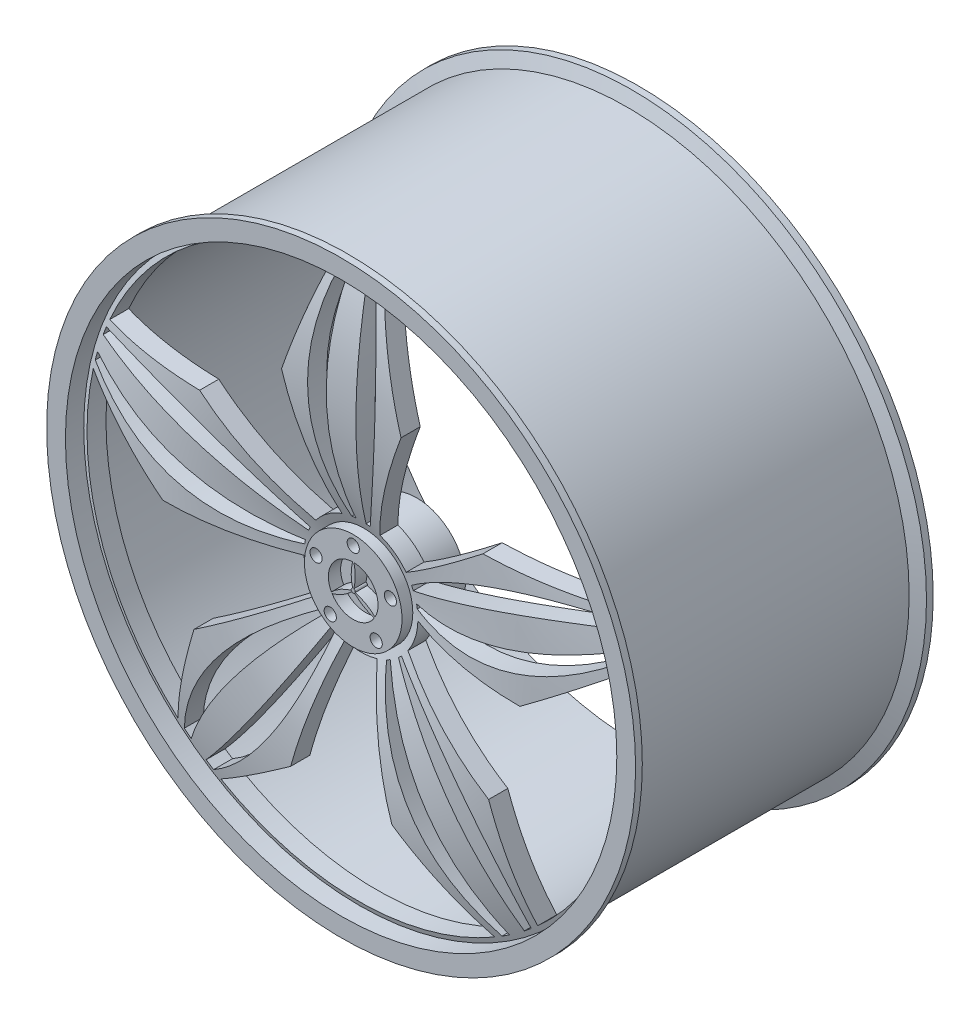
SolidWorks part; units mm, degrees
ref_plane "Front Plane" through (0, 0, 0) normal (0, 0, 1) x (1, 0, 0)
ref_plane "Top Plane" through (0, 0, 0) normal (0, 1, 0) x (1, 0, 0)
ref_plane "Right Plane" through (0, 0, 0) normal (1, 0, 0) x (0, 0, -1)
sketch "Sketch1" plane through (0, 0, 0) normal (0, 0, 1) x (1, 0, 0)
  circle A0 centre (0, 0) radius 225.9
  dimension "D1" = 451.8
sketch "Sketch2" plane through (0, 0, 0) normal (1, 0, 0) x (0, 0, -1)
  line L0 (112.7186, 230.7873) -> (-112.7186, 230.7873)
  line L1 (0, 55) -> (0, -55) construction
  line L2 (-112.7186, 230.7873) -> (-116.422, 241.3)
  line L3 (-116.422, 241.3) -> (-121.92, 241.3)
  line L4 (-121.92, 241.3) -> (-121.92, 225.9)
  line L6 (112.7186, 230.7873) -> (116.422, 241.3)
  line L7 (116.422, 241.3) -> (121.92, 241.3)
  line L8 (121.92, 241.3) -> (121.92, 225.9)
  line L10 (-121.92, 225.9) -> (121.92, 225.9)
  point P5 (0, 230.7873)
  dimension "D1" = 15.4
  dimension "D2" = 243.84
sketch "Sketch4" plane through (0, 0, 0) normal (1, 0, 0) x (0, 0, -1)
  line L0 (-133.5047, 0) -> (160.5273, 0)
revolve "Revolve1" add sketch "Sketch2" angle 360 about L0
ref_plane "Plane1" through (0, 0, 60) normal (0, 0, 1) x (1, 0, 0)
sketch "Sketch5" plane through (0, 0, 60) normal (0, 0, 1) x (1, 0, 0)
  circle A0 centre (0, 0) radius 40
extrude "Boss-Extrude1" add sketch "Sketch5" along normal blind 52 separate body
sketch "Sketch6" plane through (0, 0, 0) normal (1, 0, 0) x (0, 0, -1)
  line L0 (-121.92, 225.9) -> (-121.92, -225.9) construction
  line L1 (-106.2027, 227.9587) -> (-90.7146, 227.9587)
  line L2 (-102.0002, 36.9898) -> (-87.5596, 36.9898)
  spline S0 degree 2 poles (-102.0002, 36.9898) (-139.6143, 132.0927) (-106.2027, 227.9587) knots 0 0 0 1 1 1
  spline S1 degree 2 poles (-87.5596, 36.9898) (-123.2013, 132.2737) (-90.7146, 227.9587) knots 0 0 0 1 1 1
revolve "Revolve2" add sketch "Sketch6" angle 360 about L0
sketch "Sketch9" plane through (0, 0, 112) normal (0, 0, 1) x (1, 0, 0)
  circle A0 centre (0, 32.0205) radius 5
  circle A1 centre (30.4533, 9.8949) radius 5
  circle A2 centre (18.8212, -25.9051) radius 5
  circle A3 centre (-18.8212, -25.9051) radius 5
  circle A4 centre (-30.4533, 9.8949) radius 5
  point P12 (0, 0)
  dimension "D1" = 5
extrude "Cut-Extrude1" cut sketch "Sketch9" against normal blind 102
ref_plane "Plane2" through (0, 0, 130) normal (0, 0, 1) x (1, 0, 0)
sketch "Sketch10" plane through (0, 0, 130) normal (0, 0, 1) x (1, 0, 0)
  line L0 (116.0715, 89.196) -> (203.2814, 88.9532)
  line L1 (-15.6066, 43.9722) -> (-48.9624, 137.9536)
  line L2 (-48.9624, 137.9536) -> (-21.7821, 220.8202)
  line L3 (15.6066, 43.9722) -> (48.9624, 137.9536)
  line L4 (48.9624, 137.9536) -> (21.7821, 220.8202)
  line L5 (36.9974, 28.4309) -> (116.0715, 89.196)
  line L6 (46.6428, -1.2546) -> (146.3319, -3.936)
  line L7 (146.3319, -3.936) -> (216.7435, 47.5212)
  line L8 (120.6985, -82.8275) -> (147.4169, -165.8441)
  line L9 (38.4722, -26.401) -> (120.6985, -82.8275)
  line L10 (13.2202, -44.7476) -> (41.4757, -140.3862)
  line L11 (41.4757, -140.3862) -> (112.1728, -191.4504)
  line L12 (-41.4757, -140.3862) -> (-112.1728, -191.4504)
  line L13 (-13.2202, -44.7476) -> (-41.4757, -140.3862)
  line L14 (-38.4722, -26.401) -> (-120.6985, -82.8275)
  line L15 (-120.6985, -82.8275) -> (-147.4169, -165.8441)
  line L16 (-146.3319, -3.936) -> (-216.7435, 47.5212)
  line L17 (-46.6428, -1.2546) -> (-146.3319, -3.936)
  line L18 (-36.9974, 28.4309) -> (-116.0715, 89.196)
  line L19 (-116.0715, 89.196) -> (-203.2814, 88.9532)
  arc A0 (-15.6066, 43.9722) -> (-36.9974, 28.4309) centre (0, 0) ccw
  arc A1 (-21.7821, 220.8202) -> (-203.2814, 88.9532) centre (0, 0) ccw
  arc A2 (-7.5398, 221.7637) -> (-14.8027, 221.3976) centre (0, 0) ccw
  arc A3 (14.8027, 221.3976) -> (7.5398, 221.7637) centre (0, 0) ccw
  arc A4 (-4.1675, 46.4732) -> (-7.5398, 46.0464) centre (0, 0) ccw
  arc A5 (7.5398, 46.0464) -> (4.1675, 46.4732) centre (0, 0) ccw
  arc A6 (36.9974, 28.4309) -> (15.6066, 43.9722) centre (0, 0) ccw
  arc A7 (42.9108, 18.3246) -> (41.4628, 21.3999) centre (0, 0) ccw
  arc A8 (46.1227, 7.0583) -> (45.4864, 10.3974) centre (0, 0) ccw
  arc A9 (38.4722, -26.401) -> (46.6428, -1.2546) centre (0, 0) ccw
  arc A10 (30.6878, -35.148) -> (33.1653, -32.8205) centre (0, 0) ccw
  arc A11 (20.9656, -41.6841) -> (23.9446, -40.0472) centre (0, 0) ccw
  arc A12 (-13.2202, -44.7476) -> (13.2202, -44.7476) centre (0, 0) ccw
  arc A13 (-23.9446, -40.0472) -> (-20.9656, -41.6841) centre (0, 0) ccw
  arc A14 (-33.1653, -32.8205) -> (-30.6878, -35.148) centre (0, 0) ccw
  arc A15 (-46.6428, -1.2546) -> (-38.4722, -26.401) centre (0, 0) ccw
  arc A16 (-45.4864, 10.3974) -> (-46.1227, 7.0583) centre (0, 0) ccw
  arc A17 (-41.4628, 21.3999) -> (-42.9108, 18.3246) centre (0, 0) ccw
  arc A18 (203.2814, 88.9532) -> (21.7821, 220.8202) centre (0, 0) ccw
  arc A19 (208.5799, 75.6996) -> (205.9873, 82.4938) centre (0, 0) ccw
  arc A20 (215.1359, 54.3374) -> (213.2398, 61.358) centre (0, 0) ccw
  arc A21 (118.1586, -187.8152) -> (124.2496, -183.8424) centre (0, 0) ccw
  arc A22 (136.4493, -174.9788) -> (142.1098, -170.4136) centre (0, 0) ccw
  arc A23 (147.4169, -165.8441) -> (216.7435, 47.5212) centre (0, 0) ccw
  arc A24 (-142.1098, -170.4136) -> (-136.4493, -174.9788) centre (0, 0) ccw
  arc A25 (-124.2496, -183.8424) -> (-118.1586, -187.8152) centre (0, 0) ccw
  arc A26 (-112.1728, -191.4504) -> (112.1728, -191.4504) centre (0, 0) ccw
  arc A27 (-216.7435, 47.5212) -> (-147.4169, -165.8441) centre (0, 0) ccw
  arc A28 (-213.2398, 61.358) -> (-215.1359, 54.3374) centre (0, 0) ccw
  arc A29 (-205.9873, 82.4938) -> (-208.5799, 75.6996) centre (0, 0) ccw
  spline S0 degree 2 poles (-7.5398, 46.0464) (-43.6195, 132.703) (-14.8027, 221.3976) knots 0 0 0 1 1 1
  spline S1 degree 2 poles (-4.1675, 46.4732) (-18.32, 133.9184) (-7.5398, 221.7637) knots 0 0 0 1 1 1
  spline S2 degree 2 poles (4.1675, 46.4732) (18.32, 133.9184) (7.5398, 221.7637) knots 0 0 0 1 1 1
  spline S3 degree 2 poles (7.5398, 46.0464) (43.6195, 132.703) (14.8027, 221.3976) knots 0 0 0 1 1 1
  spline S4 degree 2 poles (41.4628, 21.3999) (112.7289, 82.492) (205.9873, 82.4938) knots 0 0 0 1 1 1
  spline S5 degree 2 poles (42.9108, 18.3246) (121.7028, 58.8064) (208.5799, 75.6996) knots 0 0 0 1 1 1
  spline S6 degree 2 poles (45.4864, 10.3974) (133.0252, 23.9598) (213.2398, 61.358) knots 0 0 0 1 1 1
  spline S7 degree 2 poles (46.1227, 7.0583) (139.6872, -0.4771) (215.1359, 54.3374) knots 0 0 0 1 1 1
  spline S8 degree 2 poles (33.1653, -32.8205) (113.2897, -81.7201) (142.1098, -170.4136) knots 0 0 0 1 1 1
  spline S9 degree 2 poles (30.6878, -35.148) (93.5364, -97.5741) (136.4493, -174.9788) knots 0 0 0 1 1 1
  spline S10 degree 2 poles (23.9446, -40.0472) (63.8941, -119.1105) (124.2496, -183.8424) knots 0 0 0 1 1 1
  spline S11 degree 2 poles (20.9656, -41.6841) (42.712, -132.9978) (118.1586, -187.8152) knots 0 0 0 1 1 1
  spline S12 degree 2 poles (-20.9656, -41.6841) (-42.712, -132.9978) (-118.1586, -187.8152) knots 0 0 0 1 1 1
  spline S13 degree 2 poles (-23.9446, -40.0472) (-63.8941, -119.1105) (-124.2496, -183.8424) knots 0 0 0 1 1 1
  spline S14 degree 2 poles (-30.6878, -35.148) (-93.5364, -97.5741) (-136.4493, -174.9788) knots 0 0 0 1 1 1
  spline S15 degree 2 poles (-33.1653, -32.8205) (-113.2897, -81.7201) (-142.1098, -170.4136) knots 0 0 0 1 1 1
  spline S16 degree 2 poles (-46.1227, 7.0583) (-139.6872, -0.4771) (-215.1359, 54.3374) knots 0 0 0 1 1 1
  spline S17 degree 2 poles (-45.4864, 10.3974) (-133.0252, 23.9598) (-213.2398, 61.358) knots 0 0 0 1 1 1
  spline S18 degree 2 poles (-42.9108, 18.3246) (-121.7028, 58.8064) (-208.5799, 75.6996) knots 0 0 0 1 1 1
  spline S19 degree 2 poles (-41.4628, 21.3999) (-112.7289, 82.492) (-205.9873, 82.4938) knots 0 0 0 1 1 1
  point P96 (0, 0)
  dimension "D1" = 5
extrude "Cut-Extrude2" cut sketch "Sketch10" against normal blind 448
sketch "Sketch11" plane through (0, 0, 112) normal (0, 0, 1) x (1, 0, 0)
  circle A0 centre (0, 0) radius 21
  circle A1 centre (0, 0) radius 1.2557
  arc A2 (-0.4876, 20.331) -> (-17.8623, -9.7225) centre (0, 0) ccw
  circle A3 centre (0, 0) radius 1.6581
  arc A4 (-17.3634, -10.5878) -> (17.3511, -10.608) centre (0, 0) ccw
  arc A5 (17.851, -9.7432) -> (0.5113, 20.3305) centre (0, 0) ccw
  spline S0 degree 2 poles (-0.4502, 1.5958) (-2.8593, 10.9394) (-0.4876, 20.331) knots 0 0 0 1 1 1
  spline S1 degree 2 poles (0.4502, 1.5958) (2.8488, 10.9366) (0.5113, 20.3305) knots 0 0 0 1 1 1
  spline S2 degree 2 poles (1.6071, -0.4081) (10.9034, -2.9935) (17.851, -9.7432) knots 0 0 0 1 1 1
  spline S3 degree 2 poles (1.157, -1.1878) (8.0469, -7.9354) (17.3511, -10.608) knots 0 0 0 1 1 1
  spline S4 degree 2 poles (-1.157, -1.1878) (-8.0442, -7.9459) (-17.3634, -10.5878) knots 0 0 0 1 1 1
  spline S5 degree 2 poles (-1.6071, -0.4081) (-10.8957, -3.0011) (-17.8623, -9.7225) knots 0 0 0 1 1 1
  point P28 (0, 0)
extrude "Cut-Extrude3" cut sketch "Sketch11" against normal blind 10 contours S5 A3 S0 A2 | A3 S2 A5 S1 | A3 S4 A4 S3
